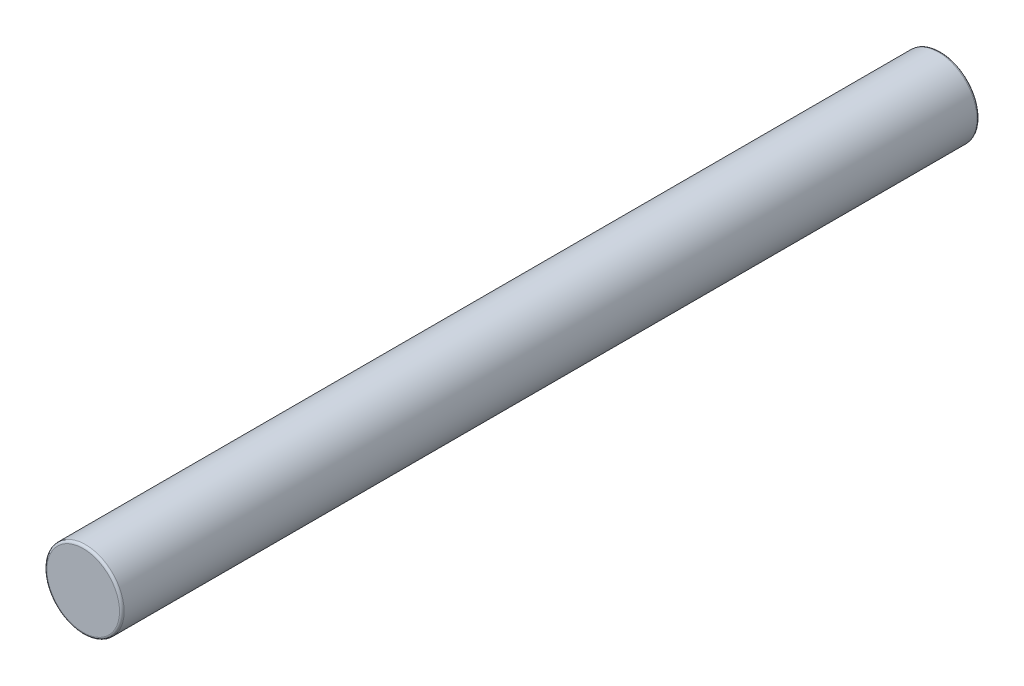
SolidWorks part; units mm, degrees
ref_plane "Front Plane" through (0, 0, 0) normal (0, 0, 1) x (1, 0, 0)
ref_plane "Top Plane" through (0, 0, 0) normal (0, 1, 0) x (1, 0, 0)
ref_plane "Right Plane" through (0, 0, 0) normal (1, 0, 0) x (0, 0, -1)
sketch "Sketch1" plane through (0, 0, 0) normal (0, 0, 1) x (1, 0, 0)
  circle A0 centre (0, 0) radius 5
extrude "Boss-Extrude1" add sketch "Sketch1" along normal mid plane 111
fillet "Fillet1" radius 0.3 2 edges at (5, 0, 55.5) (5, 0, -55.5)
